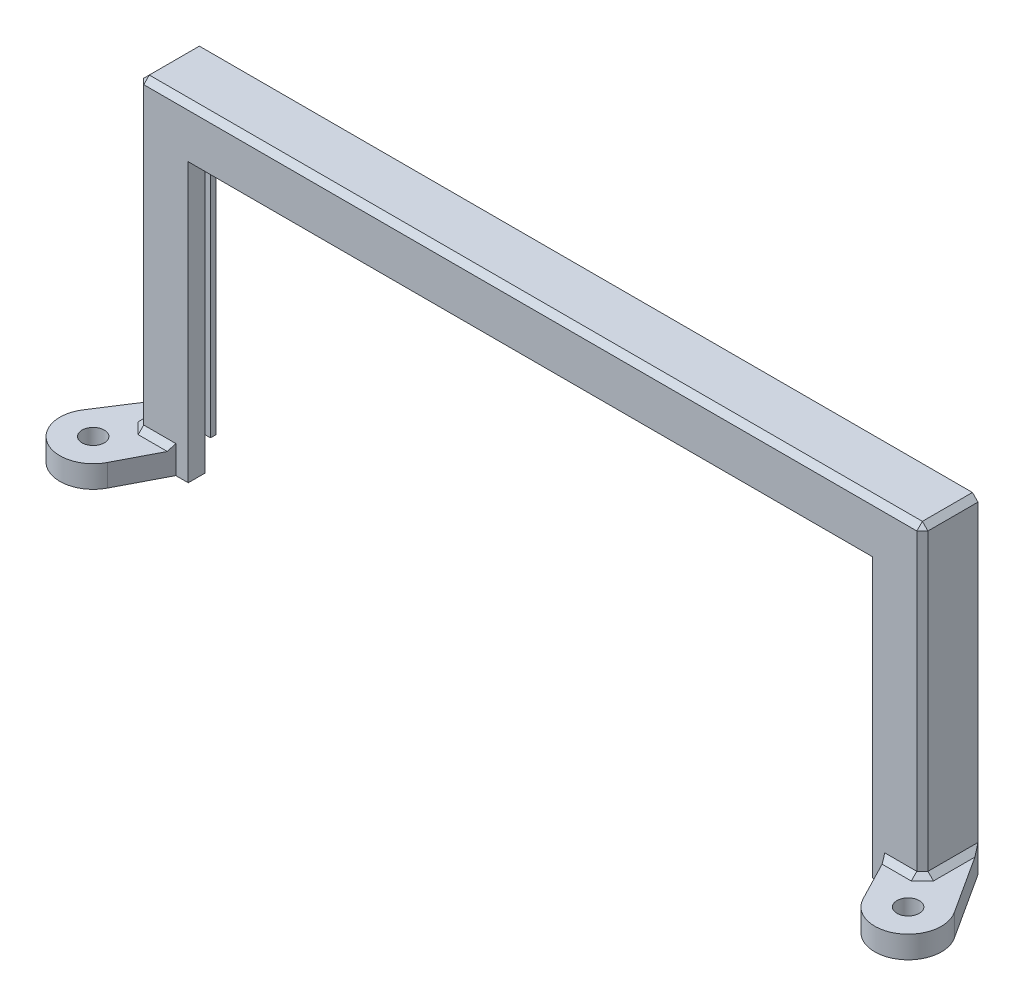
SolidWorks part; units mm, degrees
ref_plane "Front Plane" through (0, 0, 0) normal (0, 0, 1) x (1, 0, 0)
ref_plane "Top Plane" through (0, 0, 0) normal (0, 1, 0) x (1, 0, 0)
ref_plane "Right Plane" through (0, 0, 0) normal (1, 0, 0) x (0, 0, -1)
sketch "Sketch1" plane through (0, 0, 0) normal (0, 0, 1) x (1, 0, 0)
  line L1 (0, 0) -> (141, 0)
  line L2 (0, 0) -> (0, 59)
  line L3 (0, 59) -> (141, 59)
  line L4 (141, 0) -> (141, 59)
  dimension "D1" = 141
  dimension "D2" = 59
extrude "Boss-Extrude1" add sketch "Sketch1" along normal blind 10
sketch "Sketch2" plane through (0, 0, 0) normal (0, 0, -1) x (-1, 0, 0)
  line L0 (0, 0) -> (-141, 0) construction
  line L1 (-137, 0) -> (-4, 0)
  line L2 (-137, 0) -> (-137, 55)
  line L3 (-137, 55) -> (-4, 55)
  line L4 (-4, 0) -> (-4, 55)
  line L5 (0, 59) -> (0, 0) construction
  line L6 (-141, 59) -> (0, 59) construction
  line L7 (-141, 0) -> (-141, 59) construction
  dimension "D1" = 4
  dimension "D2" = 4
  dimension "D3" = 4
extrude "Cut-Extrude1" cut sketch "Sketch2" against normal blind 7
sketch "Sketch3" plane through (0, 0, 7) normal (0, 0, -1) x (-1, 0, 0)
  line L0 (-137, 0) -> (-4, 0) construction
  line L1 (-132, 0) -> (-9, 0)
  line L2 (-132, 0) -> (-132, 50)
  line L3 (-132, 50) -> (-9, 50)
  line L4 (-9, 0) -> (-9, 50)
  line L5 (-4, 55) -> (-137, 55) construction
  line L6 (-4, 0) -> (-4, 55) construction
  line L7 (-137, 55) -> (-137, 0) construction
  dimension "D1" = 5
  dimension "D2" = 5
  dimension "D3" = 5
extrude "Cut-Extrude2" cut sketch "Sketch3" against normal blind 7
sketch "Sketch4" plane through (0, 0, 0) normal (0, -1, 0) x (-1, 0, 0)
  line L0 (-4, -7) -> (-4, 0) construction
  line L1 (-4, -1) -> (-2.5, -1)
  line L2 (-4, -1) -> (-4, -5)
  line L3 (-4, -5) -> (-2.5, -5)
  line L4 (-2.5, -1) -> (-2.5, -5)
  line L5 (-9, -7) -> (-4, -7) construction
  line L6 (-70.5, -10) -> (-70.5, 0) construction
  line L7 (-9, -10) -> (-132, -10) construction
  line L8 (-4, 0) -> (-137, 0) construction
  line L9 (-138.5, -1) -> (-138.5, -5)
  line L10 (-137, -5) -> (-138.5, -5)
  line L11 (-137, -1) -> (-137, -5)
  line L12 (-137, -1) -> (-138.5, -1)
  dimension "D1" = 4
  dimension "D2" = 2
  dimension "D3" = 1.5
extrude "Cut-Extrude3" cut sketch "Sketch4" against normal blind 55
sketch "Sketch5" plane through (0, 0, 0) normal (0, -1, 0) x (-1, 0, 0)
  line L0 (0, -10) -> (-70.5, 126) construction
  line L1 (-70.5, 126) -> (-141, -10) construction
  line L2 (-4, -7) -> (-137, -7) construction
  line L3 (0, -10) -> (13.7807, -36.584) construction
  line L4 (-70.5, -10) -> (-70.5, 0) construction
  line L5 (-2.5655, -18.0882) -> (-6.7582, -10)
  line L6 (0, -10) -> (-9, -10) construction
  line L7 (7.8006, -12.0701) -> (0, 0)
  line L8 (0, 0) -> (0, -10)
  line L9 (0, -10) -> (-6.7582, -10)
  line L10 (-9, -10) -> (-132, -10) construction
  line L11 (-4, 0) -> (-137, 0) construction
  line L12 (-141, -10) -> (-154.7807, -36.584) construction
  line L13 (-141, -10) -> (-70.5, 126) construction
  line L14 (-141, -10) -> (-134.2418, -10)
  line L15 (-141, 0) -> (-141, -10)
  line L16 (-148.8006, -12.0701) -> (-141, 0)
  line L17 (-138.4345, -18.0882) -> (-134.2418, -10)
  circle A0 centre (2.7613, -15.3268) radius 2
  arc A2 (-2.5655, -18.0882) -> (7.8006, -12.0701) centre (2.7613, -15.3268) ccw
  arc A4 (-138.4345, -18.0882) -> (-148.8006, -12.0701) centre (-143.7613, -15.3268) cw
  circle A5 centre (-143.7613, -15.3268) radius 2
  point P9 (-70.5, -7)
  dimension "D3" = 4
  dimension "D1" = 133
  dimension "D2" = 6
extrude "Boss-Extrude2" add sketch "Sketch5" against normal blind 4
chamfer "Chamfer1" distance 1 angle 45 9 edges at (0, 4, 5) (137.6209, 4, 10) (3.3791, 4, 10) (141, 4, 5) (141, 59, 5) (141, 31.5, 10) (0, 59, 5) (70.5, 59, 10) (0, 31.5, 10)
